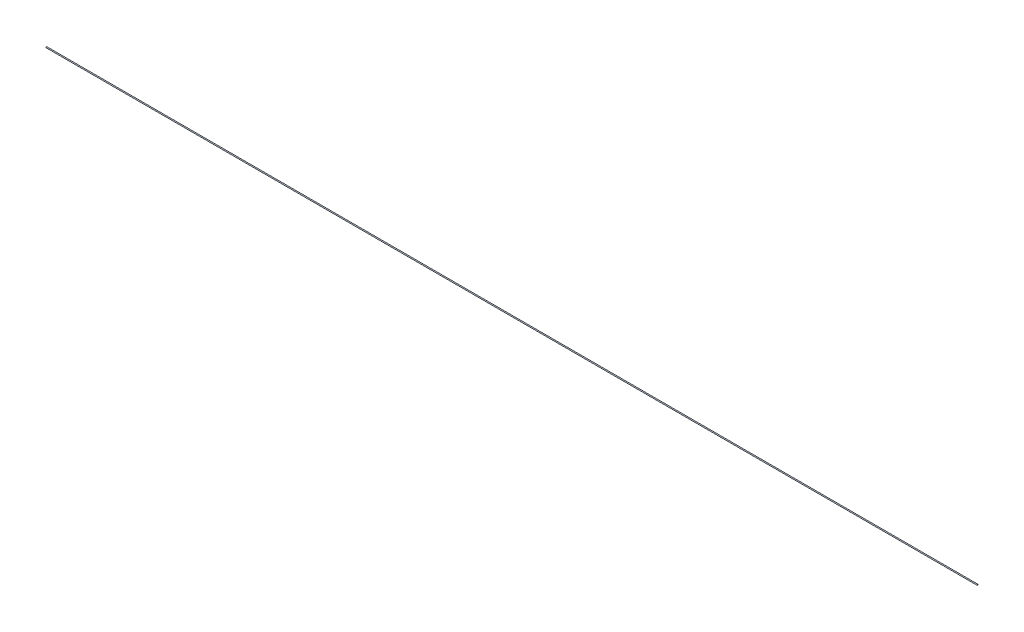
SolidWorks part; units mm, degrees
ref_plane "Front Plane" through (0, 0, 0) normal (0, 0, 1) x (1, 0, 0)
ref_plane "Top Plane" through (0, 0, 0) normal (0, 1, 0) x (1, 0, 0)
ref_plane "Right Plane" through (0, 0, 0) normal (1, 0, 0) x (0, 0, -1)
sketch "Sketch1" plane through (0, 0, 0) normal (1, 0, 0) x (0, 0, -1)
  circle A0 centre (0, 0) radius 5
  dimension "D1" = 10
extrude "Boss-Extrude1" add sketch "Sketch1" along normal blind 10000
